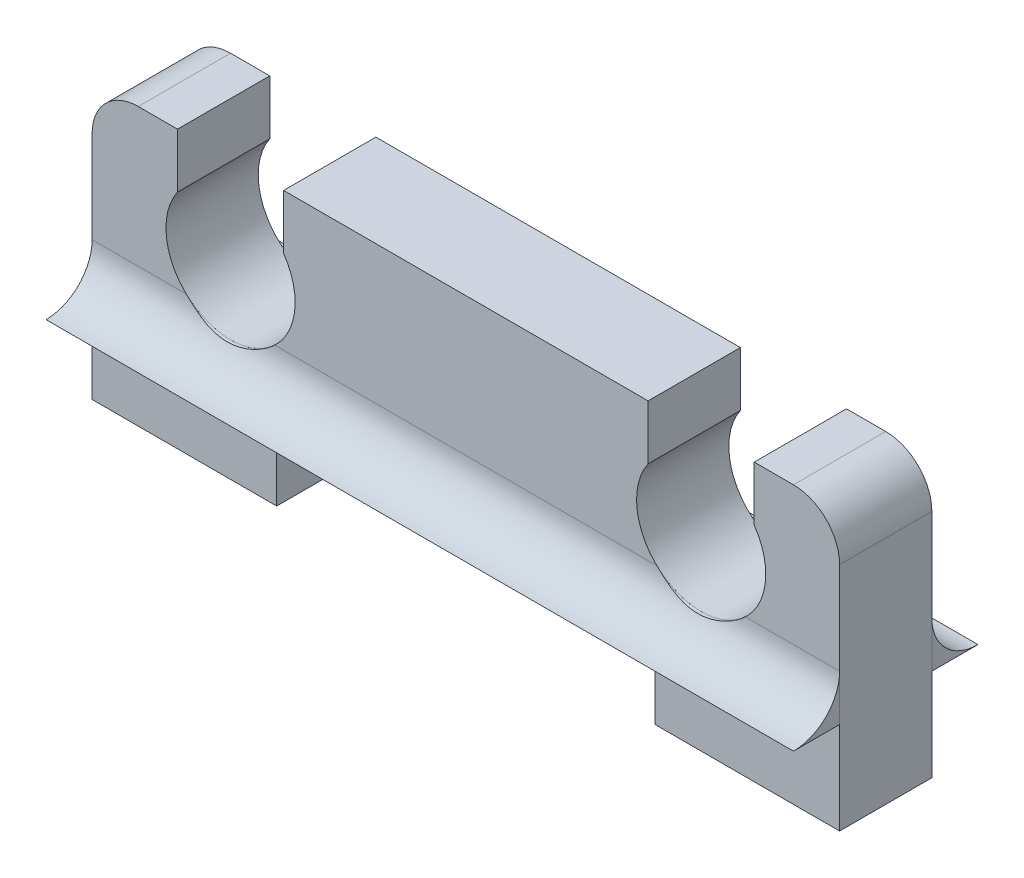
SolidWorks part; units mm, degrees
ref_plane "Front Plane" through (0, 0, 0) normal (0, 0, 1) x (1, 0, 0)
ref_plane "Top Plane" through (0, 0, 0) normal (0, 1, 0) x (1, 0, 0)
ref_plane "Right Plane" through (0, 0, 0) normal (1, 0, 0) x (0, 0, -1)
sketch "Sketch1" plane through (0, 0, 0) normal (0, 0, 1) x (1, 0, 0)
  line L0 (4, 8) -> (12.2, 8)
  line L1 (4, 4) -> (12.2, 4)
  line L2 (16.2, 0) -> (16.2, 7)
  line L3 (0, 0) -> (4, 0)
  line L4 (4, 0) -> (4, 4)
  line L5 (2, 7) -> (2, 8)
  line L6 (12.2, 8) -> (12.2, 7)
  line L7 (1, 8) -> (2, 8)
  line L8 (4, 8) -> (4, 7)
  line L9 (14.2, 8) -> (15.2, 8)
  line L10 (14.2, 8) -> (14.2, 7)
  line L11 (12.2, 0) -> (12.2, 4)
  line L12 (0, 0) -> (0, 7)
  line L13 (16.2, 0) -> (12.2, 0)
  line L14 (8.1, 4) -> (8.1, 8) construction
  arc A0 (15.2, 8) -> (16.2, 7) centre (15.2, 7) cw
  arc A1 (2, 7) -> (4, 7) centre (3, 6.0202) ccw
  arc A2 (14.2, 7) -> (12.2, 7) centre (13.2, 6.0202) cw
  arc A3 (1, 8) -> (0, 7) centre (1, 7) ccw
  dimension "D1" = 1.4
  dimension "D2" = 1
  dimension "D3" = 3
  dimension "D4" = 4
  dimension "D5" = 8.1
  dimension "D6" = 1
  dimension "D7" = 1
  dimension "D8" = 1
extrude "Boss-Extrude1" add sketch "Sketch1" along normal blind 2
sketch "Sketch2" plane through (0, 0, 0) normal (-1, 0, 0) x (0, 0, 1)
  line L0 (1, 0) -> (1, 7) construction
  line L1 (2, 7) -> (2, 0) construction
  line L2 (2, 4) -> (2, 5)
  line L3 (2, 4) -> (3, 4)
  line L4 (2, 0) -> (0, 0) construction
  line L5 (2, 7) -> (0, 7) construction
  line L6 (0, 4) -> (-1, 4)
  line L7 (0, 4) -> (0, 5)
  arc A0 (2, 5) -> (3, 4) centre (3, 5) ccw
  arc A1 (0, 5) -> (-1, 4) centre (-1, 5) cw
  dimension "D2" = 1
  dimension "D1" = 4
extrude "Boss-Extrude2" add sketch "Sketch2" against normal blind 16.2 separate body
sketch "Sketch3" plane through (0, 0, 2) normal (0, 0, 1) x (1, 0, 0)
  line L0 (0, 0) -> (0, 2)
  line L1 (0, 7) -> (0, 0) construction
  line L2 (0, 2) -> (4, 2)
  line L3 (4, 0) -> (4, 4) construction
  line L4 (4, 2) -> (4, 0)
  line L5 (4, 0) -> (0, 0)
  line L6 (8.1, 8) -> (8.1, 0) construction
  line L7 (12.2, 8) -> (4, 8) construction
  line L8 (12.2, 0) -> (16.2, 0)
  line L9 (12.2, 2) -> (12.2, 0)
  line L10 (16.2, 2) -> (12.2, 2)
  line L11 (16.2, 0) -> (16.2, 2)
extrude "Cut-Extrude1" cut sketch "Sketch3" against normal through all
sketch "Sketch5" plane through (0, 8, 0) normal (0, 1, 0) x (1, 0, 0)
  line L0 (1.85, 0) -> (4.15, 0)
  line L1 (4.4, 0) -> (1.6, 0) construction
  line L2 (12.2, 0) -> (4, 0) construction
  line L3 (3, 0) -> (3, -3) construction
  line L4 (16.2, -3) -> (0, -3) construction
  line L5 (4.15, 0) -> (4.15, -2)
  line L6 (12.2, -2) -> (4, -2) construction
  line L7 (4.15, -2) -> (1.85, -2)
  line L8 (1.85, 0) -> (1.85, -2)
  line L9 (8.1, 0) -> (8.1, -3) construction
  line L10 (14.35, 0) -> (14.35, -2)
  line L11 (12.05, -2) -> (14.35, -2)
  line L12 (12.05, 0) -> (12.05, -2)
  line L13 (14.35, 0) -> (12.05, 0)
  point P14 (3, -2)
  point P21 (13.2, -2)
  dimension "D1" = 1.15
extrude "Cut-Extrude4" cut sketch "Sketch5" against normal up to body
ref_plane "Plane1" through (0, 0, 1) normal (0, 0, 1) x (1, 0, 0)
sketch "Sketch8" plane through (0, 0, 1) normal (0, 0, 1) x (1, 0, 0)
  line L0 (8.1, 8) -> (8.1, 10.621) construction
  line L1 (12.05, 8) -> (4.15, 8) construction
  circle A0 centre (3, 6.0202) radius 1.4
  circle A1 centre (13.2, 6.0202) radius 1.4
  dimension "D1" = 2.8
extrude "Cut-Extrude6" cut sketch "Sketch8" against normal through all both and the other way through all
equation "\"D5@Sketch1\"= \"fingerWidth@parametersSketch@prostheticParameters.SLDPRT\" / 2"
equation "\"D1@Boss-Extrude2\"= \"fingerWidth@parametersSketch@prostheticParameters.SLDPRT\"'Radius of Tube Driver"
equation "\"D1@Sketch1\"= 1.25 + \"tol1@parametersSketch@prostheticParameters.SLDPRT\" / 2"
equation "\"D1@Sketch5\"= 1 + \"tol2@parametersSketch@prostheticParameters.SLDPRT\" / 2"
equation "\"D1@Sketch8\"= 2.5 + \"tol1@parametersSketch@prostheticParameters.SLDPRT\""
